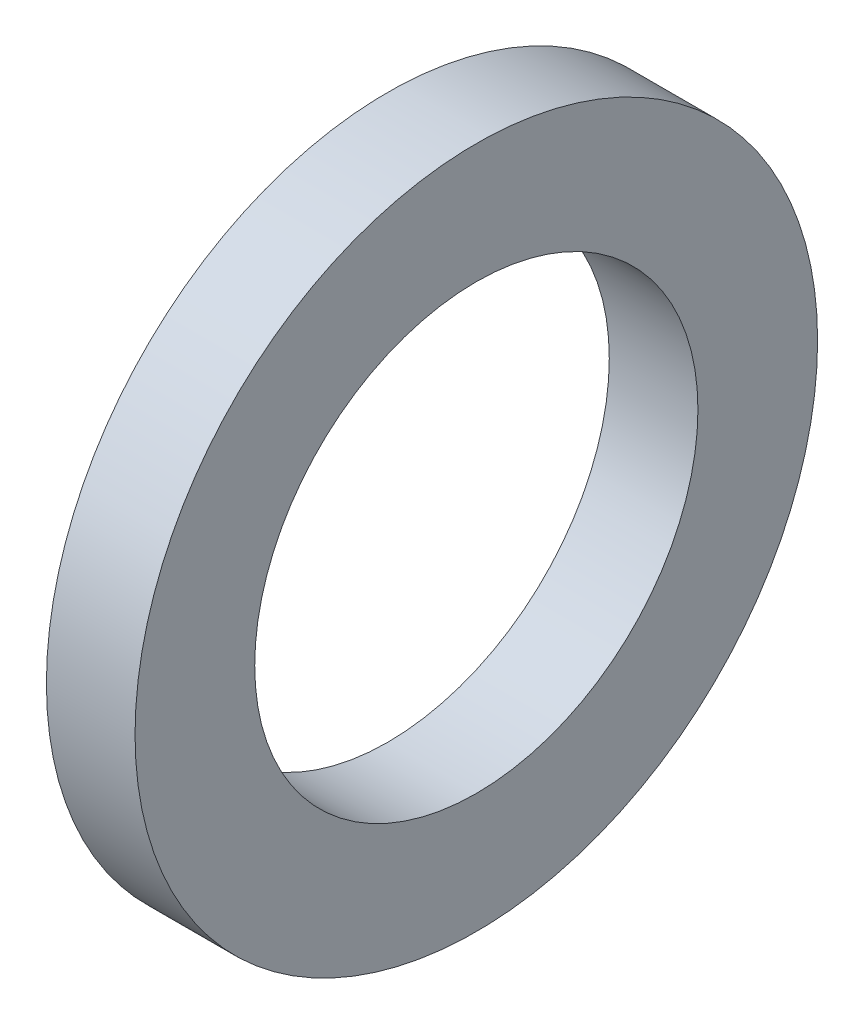
SolidWorks part; units mm, degrees
material "Cast Alloy Steel"
ref_plane "Front Plane" through (0, 0, 0) normal (0, 0, 1) x (1, 0, 0)
ref_plane "Top Plane" through (0, 0, 0) normal (0, 1, 0) x (1, 0, 0)
ref_plane "Right Plane" through (0, 0, 0) normal (1, 0, 0) x (0, 0, -1)
sketch "Sketch1" plane through (0, 0, 0) normal (0, 0, 1) x (1, 0, 0)
  line L0 (-0.5, 2.5) -> (0.5, 2.5)
  line L1 (0.5, 2.5) -> (0.5, 3.85)
  line L2 (0.5, 3.85) -> (-0.5, 3.85)
  line L3 (-0.5, 3.85) -> (-0.5, 2.5)
  line L4 (0, 0) -> (0, 2.5) construction
  line L5 (0, 0) -> (3.6016, 0) construction
  dimension "D1" = 1
  dimension "D2" = 2.5
  dimension "D3" = 3.85
revolve "Revolve1" add sketch "Sketch1" angle 360 about L5
